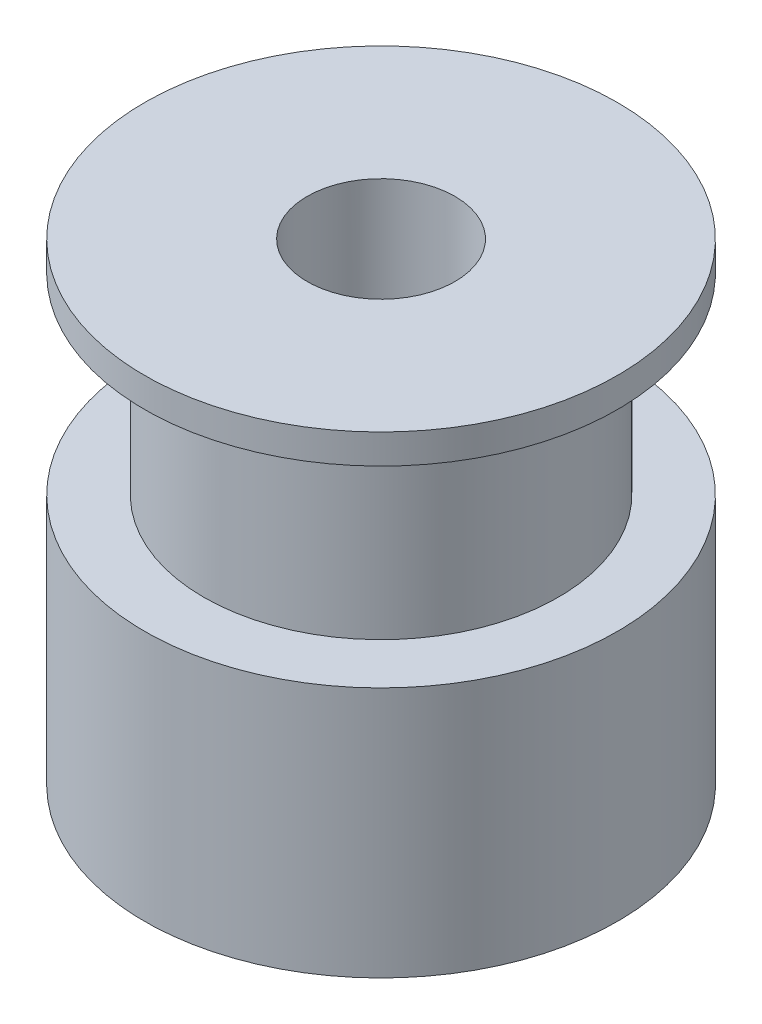
SolidWorks part; units mm, degrees
ref_plane "Plan de face" through (0, 0, 0) normal (0, 0, 1) x (1, 0, 0)
ref_plane "Plan de dessus" through (0, 0, 0) normal (0, 1, 0) x (1, 0, 0)
ref_plane "Plan de droite" through (0, 0, 0) normal (1, 0, 0) x (0, 0, -1)
sketch "Esquisse1" plane through (0, 0, 0) normal (0, 0, 1) x (1, 0, 0)
  line L0 (0, 0) -> (0, 16) construction
  line L1 (2.5, 0) -> (-2.5, 0) construction
  line L2 (8, 16) -> (-8, 16) construction
  line L3 (-2.5, 0) -> (-2.5, 16)
  line L4 (-2.5, 16) -> (-8, 16)
  line L5 (-8, 16) -> (-8, 15)
  line L6 (-8, 15) -> (-6, 15)
  line L7 (-6, 15) -> (-6, 8.5)
  line L8 (-6, 8.5) -> (-8, 8.5)
  line L9 (-8, 8.5) -> (-8, 0)
  line L10 (-8, 0) -> (-2.5, 0)
  line L11 (-8, 15) -> (-8, 8.5) construction
  line L12 (6, 15) -> (-6, 15) construction
  point P6 (0, 0)
  point P9 (0, 16)
  point P18 (0, 15)
  dimension "D1" = 16
  dimension "D2" = 5
  dimension "D3" = 16
  dimension "D4" = 12
  dimension "D5" = 6.5
  dimension "D6" = 1
revolve "Révolution1" add sketch "Esquisse1" angle 360 about L0
sketch "Esquisse2" plane through (0, 0, 0) normal (1, 0, 0) x (0, 0, -1)
  line L0 (0, 0) -> (0, 8.5) construction
  line L1 (8, 8.5) -> (-8, 8.5) construction
  circle A0 centre (0, 4.25) radius 1.5
  dimension "D1" = 3
extrude "Enlèv. mat.-Extru.1" cut sketch "Esquisse2" against normal through all
sketch "Esquisse3" plane through (0, 0, 0) normal (0, 0, 1) x (1, 0, 0)
  line L0 (0, 0) -> (0, 8.5) construction
  line L1 (8, 8.5) -> (-8, 8.5) construction
  circle A0 centre (0, 4.25) radius 1.5
  dimension "D1" = 3
extrude "Enlèv. mat.-Extru.2" cut sketch "Esquisse3" against normal through all
